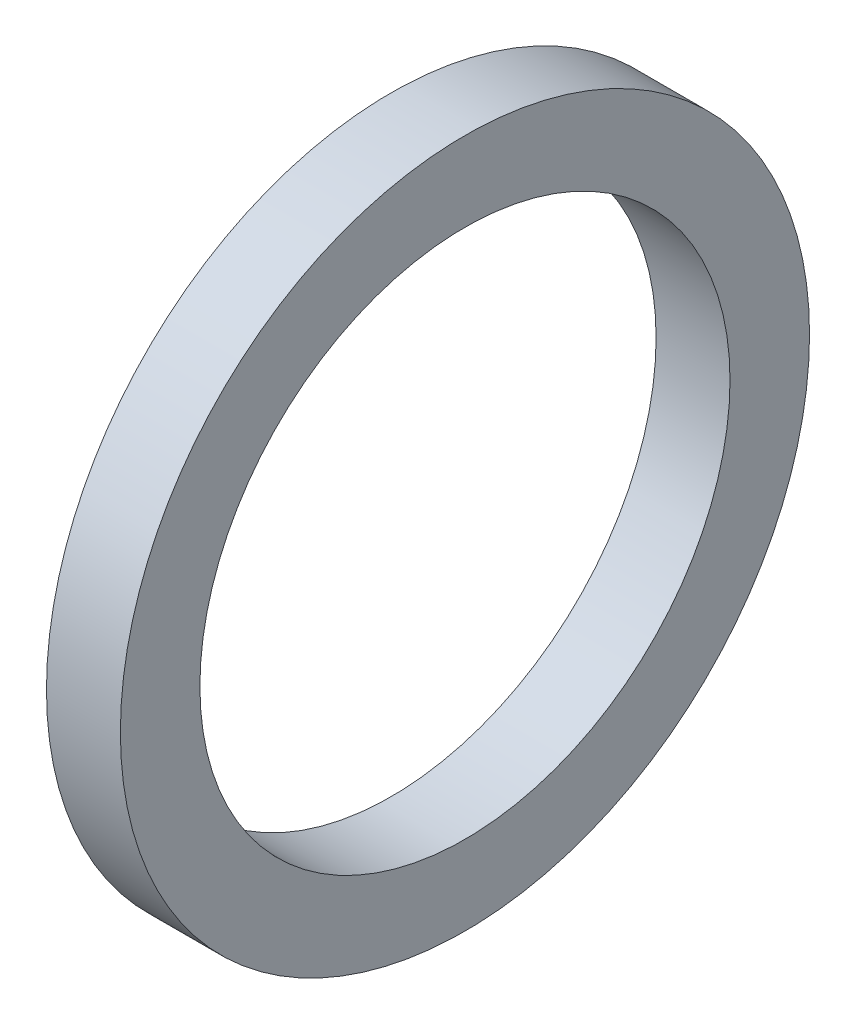
SolidWorks part; units mm, degrees
ref_plane "Front Plane" through (0, 0, 0) normal (0, 0, 1) x (1, 0, 0)
ref_plane "Top Plane" through (0, 0, 0) normal (0, 1, 0) x (1, 0, 0)
ref_plane "Right Plane" through (0, 0, 0) normal (1, 0, 0) x (0, 0, -1)
sketch "Sketch2" plane through (0, 0, 0) normal (0, 0, 1) x (1, 0, 0)
  line L0 (0, 0) -> (58.591, 0) construction
  line L2 (0, 0) -> (18.4, 0)
  line L3 (0, 0) -> (0, 2.5)
  line L4 (0, 2.5) -> (18.4, 2.5)
  line L5 (18.4, 0) -> (18.4, 2.5)
  line L6 (6.0094, 2.5) -> (6.0094, 6)
  line L11 (6.0094, 6) -> (9.9794, 6)
  line L16 (12.9794, 6) -> (12.9794, 3)
  line L17 (12.9794, 3) -> (13.6398, 3)
  line L18 (13.6398, 3) -> (13.6398, 2.5)
  line L19 (13.6398, 2.5) -> (6.0094, 2.5)
  line L22 (13.6398, 2.5) -> (16.1198, 2.5)
  line L23 (13.6398, 2.5) -> (13.6398, 4)
  line L24 (13.6398, 4) -> (16.1198, 4)
  line L25 (16.1198, 2.5) -> (16.1198, 4)
  line L27 (6.0094, 6) -> (9.9794, 6)
  line L28 (6.0094, 6) -> (6.0094, 9)
  line L29 (6.0094, 9) -> (9.9794, 9)
  line L30 (9.9794, 6) -> (9.9794, 9)
  line L31 (6.0094, 9) -> (6.0094, 8.25)
  line L32 (6.0094, 8.25) -> (5.0094, 8.25)
  line L33 (8.6609, 22.001) -> (8.6609, 12.476) construction
  line L34 (5.0094, 12.476) -> (12.3124, 12.476)
  line L35 (9.9794, 9) -> (12.3124, 9)
  line L36 (5.0094, 7.9375) -> (1.7709, 7.9375)
  line L37 (5.0094, 8.25) -> (5.0094, 12.476)
  line L38 (5.0094, 7.9375) -> (5.0094, 13.9365)
  line L39 (5.0094, 13.9365) -> (1.7709, 13.9365)
  line L40 (1.7709, 7.9375) -> (1.7709, 13.9365)
  line L41 (5.0094, 22.001) -> (12.3124, 22.001)
  line L42 (5.0094, 22.001) -> (5.0094, 30.1625)
  line L43 (5.0094, 30.1625) -> (12.3124, 30.1625)
  line L44 (12.3124, 22.001) -> (12.3124, 30.1625)
  line L49 (16.6398, 22.001) -> (16.6398, 7.5)
  line L51 (23.0198, 7.5) -> (23.0198, 6.5)
  line L54 (16.1198, 4) -> (13.6398, 4)
  line L56 (18.0398, 7.5) -> (23.0198, 7.5)
  line L57 (13.3124, 22.001) -> (16.6398, 22.001)
  line L58 (16.1198, 3.5) -> (20.0198, 3.5)
  line L59 (29.9098, 14) -> (26.9098, 11)
  line L60 (4.0094, 31.75) -> (18.0398, 31.75)
  line L61 (18.0398, 7.5) -> (23.0198, 7.5)
  line L62 (18.0398, 7.5) -> (18.0398, 12)
  line L63 (18.0398, 12) -> (23.0198, 12)
  line L64 (23.0198, 7.5) -> (23.0198, 12)
  line L65 (18.0398, 31.75) -> (18.0398, 12)
  line L66 (23.0198, 11) -> (26.9098, 11)
  line L67 (34.8098, 23) -> (31.3098, 19.5)
  line L68 (35.8098, 31) -> (38.7998, 33.99)
  line L69 (29.9098, 14) -> (29.9098, 15)
  line L70 (29.9098, 15) -> (22.9398, 15)
  line L71 (22.9398, 15) -> (21.0398, 15)
  line L72 (18.0398, 7.5) -> (16.6398, 7.5)
  line L73 (21.0398, 15) -> (21.0398, 43)
  line L74 (19.6115, 40) -> (9.6516, 40)
  line L75 (9.6516, 40) -> (4.0094, 40)
  line L76 (21.0398, 43) -> (19.6115, 43)
  line L77 (22.9398, 15) -> (29.9098, 15)
  line L78 (22.9398, 15) -> (22.9398, 21)
  line L79 (22.9398, 21) -> (29.9098, 21)
  line L80 (29.9098, 15) -> (29.9098, 21)
  line L81 (9.6516, 40) -> (19.6115, 40)
  line L82 (9.6516, 40) -> (9.6516, 50)
  line L83 (9.6516, 50) -> (19.6115, 50)
  line L84 (19.6115, 40) -> (19.6115, 50)
  line L85 (4.0094, 40) -> (4.0094, 31.75)
  line L86 (12.9794, 3) -> (12.9794, 2.5)
  line L87 (31.3098, 19.5) -> (29.9098, 19.5)
  line L88 (21.4694, 63.5) -> (21.4694, 51.308)
  line L89 (21.4694, 63.5) -> (25.9398, 63.5)
  line L90 (25.9398, 63.5) -> (25.9398, 25)
  line L91 (27.8398, 25) -> (25.9398, 25)
  line L92 (9.6516, 48) -> (8.2233, 48)
  line L93 (8.2233, 48) -> (8.2233, 53.476)
  line L94 (8.2233, 53.476) -> (19.6115, 53.476)
  line L95 (19.6115, 53.476) -> (19.6115, 50)
  line L96 (13.9174, 63.001) -> (13.9174, 53.476) construction
  line L97 (8.2233, 63.001) -> (19.6115, 63.001)
  line L98 (8.2233, 63.001) -> (8.2233, 68.2625)
  line L99 (8.2233, 68.2625) -> (19.6115, 68.2625)
  line L100 (19.6115, 63.001) -> (19.6115, 68.2625)
  line L101 (12.9794, 6) -> (11.9794, 6)
  line L102 (8.2233, 44.825) -> (4.9848, 44.825)
  line L103 (8.2233, 44.825) -> (8.2233, 54.9365)
  line L104 (8.2233, 54.9365) -> (4.9848, 54.9365)
  line L106 (9.9794, 6) -> (10.8794, 6)
  line L107 (27.8398, 25) -> (34.8098, 25)
  line L108 (34.8098, 25) -> (34.8098, 23)
  line L109 (0, 0) -> (-2, 0)
  line L110 (0, 0) -> (0, 11)
  line L111 (27.8398, 25) -> (34.8098, 25)
  line L112 (27.8398, 25) -> (27.8398, 32.5)
  line L113 (27.8398, 32.5) -> (34.8098, 32.5)
  line L114 (34.8098, 25) -> (34.8098, 32.5)
  line L115 (35.8098, 31) -> (34.8098, 31)
  line L116 (27.8398, 32.5) -> (27.8398, 64.5)
  line L117 (20.5849, 74.025) -> (6.2499, 74.025)
  line L118 (6.2499, 74.025) -> (6.2499, 76.2)
  line L119 (38.7998, 47.29) -> (30.8398, 55.25)
  line L120 (0, 11) -> (-2, 11)
  line L121 (38.7998, 43.815) -> (30.8623, 43.815)
  line L123 (-4.8152, 69.85) -> (1.5348, 76.2)
  line L124 (38.7998, 47.29) -> (38.7998, 33.99)
  line L125 (-2, 0) -> (-2, 11)
  line L126 (38.7998, 37.465) -> (30.8623, 37.465)
  line L127 (30.8623, 43.815) -> (30.8623, 37.465)
  line L128 (6.0094, 2.5) -> (6.0094, 0)
  line L129 (-0.0152, 63.5) -> (-0.0152, 30)
  line L132 (4.9848, 63.5) -> (-0.0152, 63.5)
  line L136 (-1.8152, 30) -> (-11.7752, 30)
  line L138 (-13.7752, 25.4) -> (-2, 25.4)
  line L139 (-2, 25.4) -> (-2, 11.5)
  line L140 (27.8398, 64.5) -> (20.5849, 64.5)
  line L141 (-1.8152, 30) -> (-11.7752, 30)
  line L142 (-1.8152, 30) -> (-1.8152, 39)
  line L143 (-1.8152, 39) -> (-11.7752, 39)
  line L144 (-11.7752, 30) -> (-11.7752, 39)
  line L145 (20.5849, 64.5) -> (20.5849, 74.025)
  line L146 (-12.7752, 37) -> (-12.7752, 47.29)
  line L147 (-12.7752, 37) -> (-11.7752, 37)
  line L148 (30.8398, 55.25) -> (30.8398, 76.2)
  line L149 (11.9794, 6) -> (11.9794, 5.45)
  line L154 (-2, 11.5) -> (0.5, 11.5)
  line L155 (4.9848, 60.6197) -> (24.0348, 60.6197)
  line L160 (4.9848, 60.6197) -> (4.9848, 55.8572)
  line L161 (4.9848, 55.8572) -> (24.0348, 55.8572)
  line L166 (24.0348, 60.6197) -> (24.0348, 55.8572)
  line L167 (4.9848, 60.6197) -> (24.0348, 55.8572) construction
  line L172 (4.9848, 55.8572) -> (24.0348, 60.6197) construction
  line L173 (24.0348, 62.2072) -> (25.9398, 62.2072)
  line L174 (11.9794, 5.45) -> (10.8794, 5.45)
  line L175 (10.8794, 6) -> (10.8794, 5.45)
  line L176 (24.0348, 62.2072) -> (24.0348, 54.2697)
  line L177 (24.0348, 54.2697) -> (25.9398, 54.2697)
  line L178 (25.9398, 62.2072) -> (25.9398, 54.2697)
  line L179 (24.0348, 62.2072) -> (25.9398, 54.2697) construction
  line L180 (24.0348, 54.2697) -> (25.9398, 62.2072) construction
  line L181 (3, 19.6197) -> (15.7, 19.6197)
  line L182 (3, 19.6197) -> (3, 14.8572)
  line L183 (3, 14.8572) -> (15.7, 14.8572)
  line L184 (15.7, 19.6197) -> (15.7, 14.8572)
  line L185 (3, 19.6197) -> (15.7, 14.8572) construction
  line L186 (3, 14.8572) -> (15.7, 19.6197) construction
  line L187 (15.7, 21.2072) -> (16.6398, 21.2072)
  line L188 (15.7, 21.2072) -> (15.7, 13.2697)
  line L189 (15.7, 13.2697) -> (16.6398, 13.2697)
  line L190 (16.6398, 21.2072) -> (16.6398, 13.2697)
  line L191 (15.7, 21.2072) -> (16.6398, 13.2697) construction
  line L192 (15.7, 13.2697) -> (16.6398, 21.2072) construction
  line L193 (0.5, 11.5) -> (0.5, 6.9375)
  line L194 (0.5, 6.9375) -> (1.7709, 6.9375)
  line L195 (23.0198, 6.5) -> (20.0198, 3.5)
  line L196 (4.9848, 63.5) -> (4.9848, 54.9365)
  line L197 (3, 43.825) -> (4.9848, 43.825)
  line L198 (1.7709, 6.9375) -> (1.7709, 7.9375)
  line L199 (6.0094, 0) -> (12.9794, 0)
  line L200 (12.9794, 0) -> (12.9794, 2.5)
  line L201 (18.0398, 31.75) -> (18.0398, 35.875)
  line L202 (18.0398, 35.875) -> (21.0398, 35.875)
  line L203 (30.8398, 76.2) -> (6.2499, 76.2)
  line L204 (2.8049, 69.85) -> (7.2499, 69.85) construction
  line L205 (7.2499, 67.4688) -> (26.2999, 67.4688)
  line L206 (7.2499, 74.025) -> (7.2499, 64.5)
  line L207 (7.2499, 64.5) -> (-1.8152, 64.5)
  line L208 (-1.8152, 64.5) -> (-1.8152, 39)
  line L209 (-12.7752, 47.29) -> (-4.8152, 55.25)
  line L210 (-4.8152, 55.25) -> (-4.8152, 69.85)
  line L211 (7.2499, 67.4688) -> (7.2499, 72.2312)
  line L212 (7.2499, 72.2312) -> (26.2999, 72.2313)
  line L213 (26.2999, 67.4688) -> (26.2999, 72.2313)
  line L214 (26.2999, 73.8187) -> (30.8398, 73.8187)
  line L215 (26.2999, 73.8187) -> (26.2999, 65.8813)
  line L216 (26.2999, 65.8813) -> (30.8398, 65.8813)
  line L217 (30.8398, 73.8187) -> (30.8398, 65.8813)
  line L218 (2.8049, 72.2313) -> (25.0299, 72.2313)
  line L219 (2.8049, 72.2313) -> (2.8049, 67.4687)
  line L220 (2.8049, 67.4687) -> (25.0299, 67.4687)
  line L221 (25.0299, 72.2313) -> (25.0299, 67.4687)
  line L222 (25.0299, 69.85) -> (20.5849, 69.85) construction
  line L223 (21.4694, 51.308) -> (22.9398, 51.308)
  line L224 (22.9398, 51.308) -> (22.9398, 21)
  line L225 (13.6398, 4) -> (13.6398, 12.2697)
  line L226 (13.6398, 12.2697) -> (13.3124, 12.2697)
  line L227 (13.3124, 12.2697) -> (13.3124, 22.001)
  line L228 (12.3124, 9) -> (12.3124, 12.476)
  line L229 (-1.8152, 30) -> (-0.0152, 30)
  line L230 (8.2233, 65.6317) -> (2.8049, 65.6317) construction
  line L231 (19.6115, 65.6317) -> (25.0299, 65.6317) construction
  line L232 (1.5348, 76.2) -> (6.2499, 76.2)
  line L233 (-11.7752, 30) -> (-13.7752, 30)
  line L234 (-13.7752, 30) -> (-13.7752, 25.4)
  line L235 (3, 13.9365) -> (3, 43.825)
  line L236 (4.9848, 54.9365) -> (4.9848, 44.825)
  line L237 (4.9848, 43.825) -> (4.9848, 44.825)
  circle A0 centre (26.8898, 25.95) radius 0.95
  circle A1 centre (21.9898, 15.95) radius 0.95
  circle A2 centre (17.3398, 8.2) radius 0.7
  circle A3 centre (10.4294, 6.45) radius 0.45
  circle A4 centre (-0.9152, 30.9) radius 0.9
  point P7 (24.9873, 58.2385)
  point P131 (16.1699, 17.2385)
  point P135 (14.5098, 58.2385)
  point P146 (9.35, 17.2385)
sketch "Sketch3" plane through (0, 0, 0) normal (0, 0, 1) x (1, 0, 0)
  line L0 (27.8398, 25) -> (34.8098, 25) construction
  line L1 (27.8398, 25) -> (27.8398, 32.5) construction
  line L2 (34.8098, 25) -> (34.8098, 32.5) construction
  line L3 (27.8398, 32.5) -> (34.8098, 32.5) construction
  line L4 (27.8398, 25) -> (34.8098, 25)
  line L5 (27.8398, 25) -> (27.8398, 32.5)
  line L6 (34.8098, 25) -> (34.8098, 32.5)
  line L7 (27.8398, 32.5) -> (34.8098, 32.5)
revolve "Revolve1" add sketch "Sketch3" angle 360 about L0
